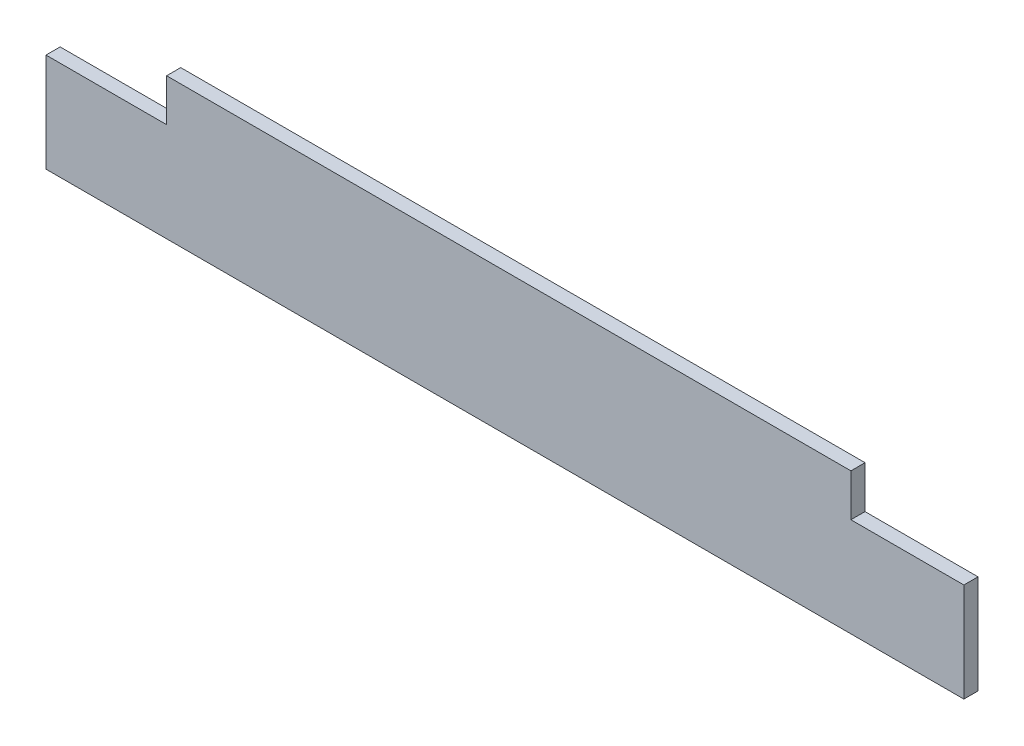
SolidWorks part; units mm, degrees
ref_plane "Plan de face" through (0, 0, 0) normal (0, 0, 1) x (1, 0, 0)
ref_plane "Plan de dessus" through (0, 0, 0) normal (0, 1, 0) x (1, 0, 0)
ref_plane "Plan de droite" through (0, 0, 0) normal (1, 0, 0) x (0, 0, -1)
sketch "Esquisse1" plane through (0, 0, 0) normal (0, 0, 1) x (1, 0, 0)
  line L5 (-325, -219.4526) -> (325, -219.4526)
  line L6 (-325, -219.4526) -> (-325, -119.4526)
  line L7 (-325, -119.4526) -> (325, -119.4526)
  line L8 (325, -219.4526) -> (325, -119.4526)
  line L9 (-325, -219.4526) -> (325, -119.4526) construction
  line L10 (-325, -119.4526) -> (325, -219.4526) construction
  line L11 (-325, -119.4526) -> (-239.5985, -119.4526)
  line L12 (-325, -119.4526) -> (-325, -149.4526)
  line L13 (-325, -149.4526) -> (-239.5985, -149.4526)
  line L14 (-239.5985, -119.4526) -> (-239.5985, -149.4526)
  line L15 (325, -119.4526) -> (245, -119.4526)
  line L16 (325, -119.4526) -> (325, -149.4526)
  line L17 (325, -149.4526) -> (245, -149.4526)
  line L18 (245, -119.4526) -> (245, -149.4526)
  dimension "D1" = 650
  dimension "D2" = 100
  dimension "D3" = 80
  dimension "D4" = 30
  dimension "D5" = 30
extrude "Boss.-Extru.1" add sketch "Esquisse1" along normal blind 10 contours L18 L7 L14 L13 L6 L5 L8 L17
